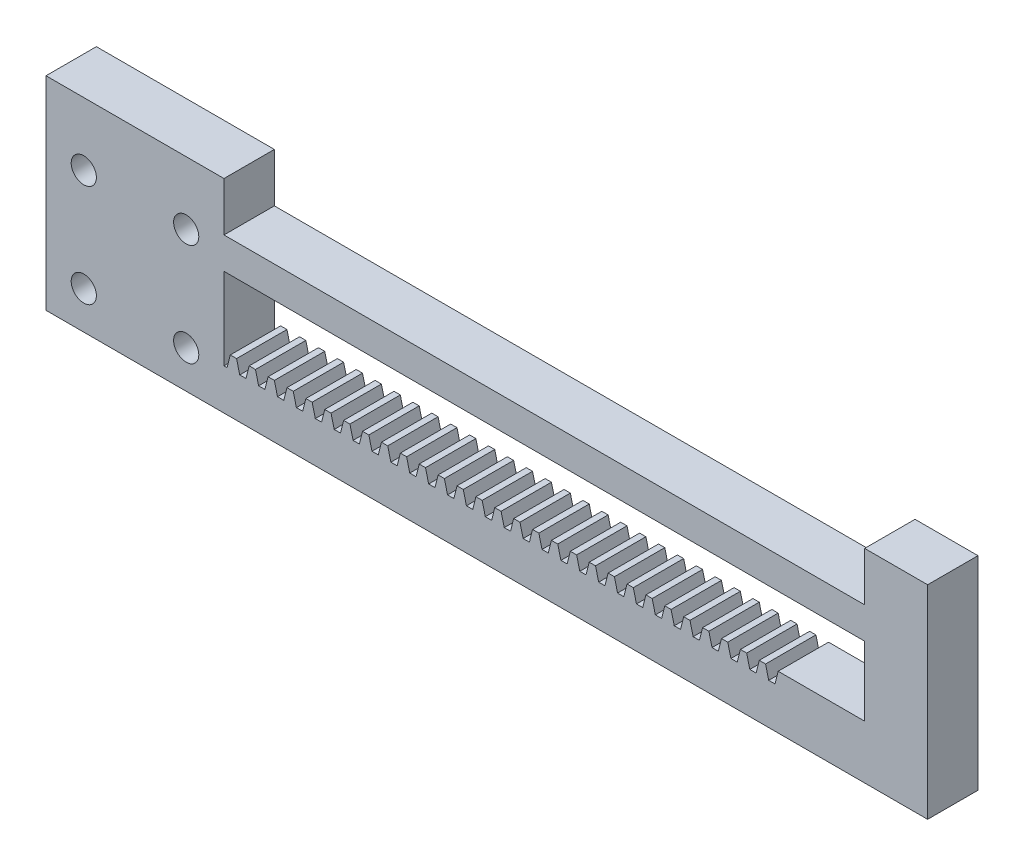
SolidWorks part; units mm, degrees
ref_plane "Front Plane" through (0, 0, 0) normal (0, 0, 1) x (1, 0, 0)
ref_plane "Top Plane" through (0, 0, 0) normal (0, 1, 0) x (1, 0, 0)
ref_plane "Right Plane" through (0, 0, 0) normal (1, 0, 0) x (0, 0, -1)
sketch "Sketch1" plane through (0, 0, 0) normal (0, 0, 1) x (1, 0, 0)
  line L1 (-111.7365, -14.1317) -> (-9.9686, -14.1317)
  line L2 (-111.7365, -7.6317) -> (-111.7365, 5.3683)
  line L4 (-10, -5.6317) -> (-10, 5.3683)
  line L5 (-111.7365, -7.6317) -> (-111.2365, -7.6317)
  line L6 (-111.2365, -7.6317) -> (-110.7365, -5.6317)
  line L7 (-111.7365, 18.1317) -> (-140, 18.1317)
  line L9 (-111.7365, -14.1317) -> (-140, -14.1317)
  line L15 (-10, 18.1317) -> (0, 18.1317) construction
  line L16 (-10, 18.1317) -> (-10, 10.3683) construction
  line L17 (-9.9686, -14.1317) -> (0, -14.1317) construction
  line L18 (0, 18.1317) -> (0, -14.1317)
  line L21 (-10, 18.1317) -> (0, 18.1317)
  line L22 (-10, -7.6317) -> (-111.7365, -7.6317) construction
  line L163 (-9.9686, -14.1317) -> (0, -14.1317)
  line L164 (-140, -14.1317) -> (-140, 18.1317)
  line L166 (-111.7365, -7.6317) -> (-111.7365, -14.1317) construction
  line L167 (-117.7365, -8.1317) -> (-134, 8.1317) construction
  line L168 (-134, -8.1317) -> (-117.7365, 8.1317) construction
  line L169 (-23.7365, -5.6317) -> (-10, -5.6317)
  line L170 (-135.8069, 0) -> (-111.7365, 0) construction
  line L171 (-111.7365, 5.3683) -> (-10, 5.3683)
  line L181 (-110.7365, -5.6317) -> (-109.7365, -5.6317)
  line L182 (-109.7365, -5.6317) -> (-109.2365, -7.6317)
  line L183 (-109.2365, -7.6317) -> (-108.7365, -7.6317)
  line L185 (-111.2365, -7.6317) -> (-109.2365, -7.6317) construction
  line L187 (-110.2365, -7.6317) -> (-110.2365, -5.6317) construction
  line L189 (-108.7365, -7.6317) -> (-108.2365, -7.6317)
  line L190 (-108.2365, -7.6317) -> (-107.7365, -5.6317)
  line L191 (-107.7365, -5.6317) -> (-106.7365, -5.6317)
  line L192 (-106.7365, -5.6317) -> (-106.2365, -7.6317)
  line L193 (-106.2365, -7.6317) -> (-105.7365, -7.6317)
  line L194 (-105.7365, -7.6317) -> (-105.2365, -7.6317)
  line L195 (-105.2365, -7.6317) -> (-104.7365, -5.6317)
  line L196 (-104.7365, -5.6317) -> (-103.7365, -5.6317)
  line L197 (-103.7365, -5.6317) -> (-103.2365, -7.6317)
  line L198 (-103.2365, -7.6317) -> (-102.7365, -7.6317)
  line L199 (-102.7365, -7.6317) -> (-102.2365, -7.6317)
  line L200 (-102.2365, -7.6317) -> (-101.7365, -5.6317)
  line L201 (-101.7365, -5.6317) -> (-100.7365, -5.6317)
  line L202 (-100.7365, -5.6317) -> (-100.2365, -7.6317)
  line L203 (-100.2365, -7.6317) -> (-99.7365, -7.6317)
  line L204 (-99.7365, -7.6317) -> (-99.2365, -7.6317)
  line L205 (-99.2365, -7.6317) -> (-98.7365, -5.6317)
  line L206 (-98.7365, -5.6317) -> (-97.7365, -5.6317)
  line L207 (-97.7365, -5.6317) -> (-97.2365, -7.6317)
  line L208 (-97.2365, -7.6317) -> (-96.7365, -7.6317)
  line L209 (-96.7365, -7.6317) -> (-96.2365, -7.6317)
  line L210 (-96.2365, -7.6317) -> (-95.7365, -5.6317)
  line L211 (-95.7365, -5.6317) -> (-94.7365, -5.6317)
  line L212 (-94.7365, -5.6317) -> (-94.2365, -7.6317)
  line L213 (-94.2365, -7.6317) -> (-93.7365, -7.6317)
  line L214 (-93.7365, -7.6317) -> (-93.2365, -7.6317)
  line L215 (-93.2365, -7.6317) -> (-92.7365, -5.6317)
  line L216 (-92.7365, -5.6317) -> (-91.7365, -5.6317)
  line L217 (-91.7365, -5.6317) -> (-91.2365, -7.6317)
  line L218 (-91.2365, -7.6317) -> (-90.7365, -7.6317)
  line L219 (-90.7365, -7.6317) -> (-90.2365, -7.6317)
  line L220 (-90.2365, -7.6317) -> (-89.7365, -5.6317)
  line L221 (-89.7365, -5.6317) -> (-88.7365, -5.6317)
  line L222 (-88.7365, -5.6317) -> (-88.2365, -7.6317)
  line L223 (-88.2365, -7.6317) -> (-87.7365, -7.6317)
  line L224 (-87.7365, -7.6317) -> (-87.2365, -7.6317)
  line L225 (-87.2365, -7.6317) -> (-86.7365, -5.6317)
  line L226 (-86.7365, -5.6317) -> (-85.7365, -5.6317)
  line L227 (-85.7365, -5.6317) -> (-85.2365, -7.6317)
  line L228 (-85.2365, -7.6317) -> (-84.7365, -7.6317)
  line L229 (-84.7365, -7.6317) -> (-84.2365, -7.6317)
  line L230 (-84.2365, -7.6317) -> (-83.7365, -5.6317)
  line L231 (-83.7365, -5.6317) -> (-82.7365, -5.6317)
  line L232 (-82.7365, -5.6317) -> (-82.2365, -7.6317)
  line L233 (-82.2365, -7.6317) -> (-81.7365, -7.6317)
  line L234 (-81.7365, -7.6317) -> (-81.2365, -7.6317)
  line L235 (-81.2365, -7.6317) -> (-80.7365, -5.6317)
  line L236 (-80.7365, -5.6317) -> (-79.7365, -5.6317)
  line L237 (-79.7365, -5.6317) -> (-79.2365, -7.6317)
  line L238 (-79.2365, -7.6317) -> (-78.7365, -7.6317)
  line L239 (-78.7365, -7.6317) -> (-78.2365, -7.6317)
  line L240 (-78.2365, -7.6317) -> (-77.7365, -5.6317)
  line L241 (-77.7365, -5.6317) -> (-76.7365, -5.6317)
  line L242 (-76.7365, -5.6317) -> (-76.2365, -7.6317)
  line L243 (-76.2365, -7.6317) -> (-75.7365, -7.6317)
  line L244 (-75.7365, -7.6317) -> (-75.2365, -7.6317)
  line L245 (-75.2365, -7.6317) -> (-74.7365, -5.6317)
  line L246 (-74.7365, -5.6317) -> (-73.7365, -5.6317)
  line L247 (-73.7365, -5.6317) -> (-73.2365, -7.6317)
  line L248 (-73.2365, -7.6317) -> (-72.7365, -7.6317)
  line L249 (-72.7365, -7.6317) -> (-72.2365, -7.6317)
  line L250 (-72.2365, -7.6317) -> (-71.7365, -5.6317)
  line L251 (-71.7365, -5.6317) -> (-70.7365, -5.6317)
  line L252 (-70.7365, -5.6317) -> (-70.2365, -7.6317)
  line L253 (-70.2365, -7.6317) -> (-69.7365, -7.6317)
  line L254 (-69.7365, -7.6317) -> (-69.2365, -7.6317)
  line L255 (-69.2365, -7.6317) -> (-68.7365, -5.6317)
  line L256 (-68.7365, -5.6317) -> (-67.7365, -5.6317)
  line L257 (-67.7365, -5.6317) -> (-67.2365, -7.6317)
  line L258 (-67.2365, -7.6317) -> (-66.7365, -7.6317)
  line L259 (-66.7365, -7.6317) -> (-66.2365, -7.6317)
  line L260 (-66.2365, -7.6317) -> (-65.7365, -5.6317)
  line L261 (-65.7365, -5.6317) -> (-64.7365, -5.6317)
  line L262 (-64.7365, -5.6317) -> (-64.2365, -7.6317)
  line L263 (-64.2365, -7.6317) -> (-63.7365, -7.6317)
  line L264 (-63.7365, -7.6317) -> (-63.2365, -7.6317)
  line L265 (-63.2365, -7.6317) -> (-62.7365, -5.6317)
  line L266 (-62.7365, -5.6317) -> (-61.7365, -5.6317)
  line L267 (-61.7365, -5.6317) -> (-61.2365, -7.6317)
  line L268 (-61.2365, -7.6317) -> (-60.7365, -7.6317)
  line L269 (-60.7365, -7.6317) -> (-60.2365, -7.6317)
  line L270 (-60.2365, -7.6317) -> (-59.7365, -5.6317)
  line L271 (-59.7365, -5.6317) -> (-58.7365, -5.6317)
  line L272 (-58.7365, -5.6317) -> (-58.2365, -7.6317)
  line L273 (-58.2365, -7.6317) -> (-57.7365, -7.6317)
  line L274 (-57.7365, -7.6317) -> (-57.2365, -7.6317)
  line L275 (-57.2365, -7.6317) -> (-56.7365, -5.6317)
  line L276 (-56.7365, -5.6317) -> (-55.7365, -5.6317)
  line L277 (-55.7365, -5.6317) -> (-55.2365, -7.6317)
  line L278 (-55.2365, -7.6317) -> (-54.7365, -7.6317)
  line L279 (-54.7365, -7.6317) -> (-54.2365, -7.6317)
  line L280 (-54.2365, -7.6317) -> (-53.7365, -5.6317)
  line L281 (-53.7365, -5.6317) -> (-52.7365, -5.6317)
  line L282 (-52.7365, -5.6317) -> (-52.2365, -7.6317)
  line L283 (-52.2365, -7.6317) -> (-51.7365, -7.6317)
  line L284 (-51.7365, -7.6317) -> (-51.2365, -7.6317)
  line L285 (-51.2365, -7.6317) -> (-50.7365, -5.6317)
  line L286 (-50.7365, -5.6317) -> (-49.7365, -5.6317)
  line L287 (-49.7365, -5.6317) -> (-49.2365, -7.6317)
  line L288 (-49.2365, -7.6317) -> (-48.7365, -7.6317)
  line L289 (-48.7365, -7.6317) -> (-48.2365, -7.6317)
  line L290 (-48.2365, -7.6317) -> (-47.7365, -5.6317)
  line L291 (-47.7365, -5.6317) -> (-46.7365, -5.6317)
  line L292 (-46.7365, -5.6317) -> (-46.2365, -7.6317)
  line L293 (-46.2365, -7.6317) -> (-45.7365, -7.6317)
  line L294 (-45.7365, -7.6317) -> (-45.2365, -7.6317)
  line L295 (-45.2365, -7.6317) -> (-44.7365, -5.6317)
  line L296 (-44.7365, -5.6317) -> (-43.7365, -5.6317)
  line L297 (-43.7365, -5.6317) -> (-43.2365, -7.6317)
  line L298 (-43.2365, -7.6317) -> (-42.7365, -7.6317)
  line L299 (-42.7365, -7.6317) -> (-42.2365, -7.6317)
  line L300 (-42.2365, -7.6317) -> (-41.7365, -5.6317)
  line L301 (-41.7365, -5.6317) -> (-40.7365, -5.6317)
  line L302 (-40.7365, -5.6317) -> (-40.2365, -7.6317)
  line L303 (-40.2365, -7.6317) -> (-39.7365, -7.6317)
  line L304 (-39.7365, -7.6317) -> (-39.2365, -7.6317)
  line L305 (-39.2365, -7.6317) -> (-38.7365, -5.6317)
  line L306 (-38.7365, -5.6317) -> (-37.7365, -5.6317)
  line L307 (-37.7365, -5.6317) -> (-37.2365, -7.6317)
  line L308 (-37.2365, -7.6317) -> (-36.7365, -7.6317)
  line L309 (-36.7365, -7.6317) -> (-36.2365, -7.6317)
  line L310 (-36.2365, -7.6317) -> (-35.7365, -5.6317)
  line L311 (-35.7365, -5.6317) -> (-34.7365, -5.6317)
  line L312 (-34.7365, -5.6317) -> (-34.2365, -7.6317)
  line L313 (-34.2365, -7.6317) -> (-33.7365, -7.6317)
  line L314 (-33.7365, -7.6317) -> (-33.2365, -7.6317)
  line L315 (-33.2365, -7.6317) -> (-32.7365, -5.6317)
  line L316 (-32.7365, -5.6317) -> (-31.7365, -5.6317)
  line L317 (-31.7365, -5.6317) -> (-31.2365, -7.6317)
  line L318 (-31.2365, -7.6317) -> (-30.7365, -7.6317)
  line L319 (-30.7365, -7.6317) -> (-30.2365, -7.6317)
  line L320 (-30.2365, -7.6317) -> (-29.7365, -5.6317)
  line L321 (-29.7365, -5.6317) -> (-28.7365, -5.6317)
  line L322 (-28.7365, -5.6317) -> (-28.2365, -7.6317)
  line L323 (-28.2365, -7.6317) -> (-27.7365, -7.6317)
  line L324 (-27.7365, -7.6317) -> (-27.2365, -7.6317)
  line L325 (-27.2365, -7.6317) -> (-26.7365, -5.6317)
  line L326 (-26.7365, -5.6317) -> (-25.7365, -5.6317)
  line L327 (-25.7365, -5.6317) -> (-25.2365, -7.6317)
  line L328 (-25.2365, -7.6317) -> (-24.7365, -7.6317)
  line L329 (-24.7365, -7.6317) -> (-24.2365, -7.6317)
  line L330 (-24.2365, -7.6317) -> (-23.7365, -5.6317)
  line L415 (13.7635, -7.6317) -> (14.2635, -7.6317) [skipped]
  line L416 (14.2635, -7.6317) -> (14.7635, -7.6317) [skipped]
  line L417 (14.7635, -7.6317) -> (15.2635, -5.6317) [skipped]
  line L418 (15.2635, -5.6317) -> (16.2635, -5.6317) [skipped]
  line L419 (16.2635, -5.6317) -> (16.7635, -7.6317) [skipped]
  line L420 (16.7635, -7.6317) -> (17.2635, -7.6317) [skipped]
  line L421 (17.2635, -7.6317) -> (17.7635, -7.6317) [skipped]
  line L422 (17.7635, -7.6317) -> (18.2635, -5.6317) [skipped]
  line L423 (18.2635, -5.6317) -> (19.2635, -5.6317) [skipped]
  line L424 (19.2635, -5.6317) -> (19.7635, -7.6317) [skipped]
  line L425 (19.7635, -7.6317) -> (20.2635, -7.6317) [skipped]
  line L426 (20.2635, -7.6317) -> (20.7635, -7.6317) [skipped]
  line L427 (20.7635, -7.6317) -> (21.2635, -5.6317) [skipped]
  line L428 (21.2635, -5.6317) -> (22.2635, -5.6317) [skipped]
  line L429 (22.2635, -5.6317) -> (22.7635, -7.6317) [skipped]
  line L430 (22.7635, -7.6317) -> (23.2635, -7.6317) [skipped]
  line L431 (23.2635, -7.6317) -> (23.7635, -7.6317) [skipped]
  line L432 (23.7635, -7.6317) -> (24.2635, -5.6317) [skipped]
  line L433 (24.2635, -5.6317) -> (25.2635, -5.6317) [skipped]
  line L434 (25.2635, -5.6317) -> (25.7635, -7.6317) [skipped]
  line L435 (25.7635, -7.6317) -> (26.2635, -7.6317) [skipped]
  line L436 (13.2635, -5.6317) -> (13.7635, -7.6317) [skipped]
  line L437 (11.7635, -7.6317) -> (12.2635, -5.6317) [skipped]
  line L438 (12.2635, -5.6317) -> (13.2635, -5.6317) [skipped]
  line L440 (8.7635, -7.6317) -> (9.2635, -5.6317) [skipped]
  line L441 (9.2635, -5.6317) -> (10.2635, -5.6317) [skipped]
  line L442 (10.2635, -5.6317) -> (10.7635, -7.6317) [skipped]
  line L443 (10.7635, -7.6317) -> (11.2635, -7.6317) [skipped]
  line L444 (11.2635, -7.6317) -> (11.7635, -7.6317) [skipped]
  line L445 (8.2635, -7.6317) -> (8.7635, -7.6317) [skipped]
  line L446 (7.7635, -7.6317) -> (8.2635, -7.6317) [skipped]
  line L447 (-111.7365, 10.3683) -> (-10, 10.3683)
  line L448 (-111.7365, 10.3683) -> (-111.7365, 18.1317)
  line L449 (-10.7365, -5.6317) -> (-10.2365, -7.6317) [skipped]
  line L450 (-10.2365, -7.6317) -> (-9.7365, -7.6317) [skipped]
  line L451 (-9.7365, -7.6317) -> (-9.2365, -7.6317) [skipped]
  line L452 (-9.2365, -7.6317) -> (-8.7365, -5.6317) [skipped]
  line L453 (-8.7365, -5.6317) -> (-7.7365, -5.6317) [skipped]
  line L454 (-7.7365, -5.6317) -> (-7.2365, -7.6317) [skipped]
  line L455 (-7.2365, -7.6317) -> (-6.7365, -7.6317) [skipped]
  line L456 (-6.7365, -7.6317) -> (-6.2365, -7.6317) [skipped]
  line L457 (-6.2365, -7.6317) -> (-5.7365, -5.6317) [skipped]
  line L458 (-5.7365, -5.6317) -> (-4.7365, -5.6317) [skipped]
  line L459 (-4.7365, -5.6317) -> (-4.2365, -7.6317) [skipped]
  line L460 (-4.2365, -7.6317) -> (-3.7365, -7.6317) [skipped]
  line L461 (-3.7365, -7.6317) -> (-3.2365, -7.6317) [skipped]
  line L462 (-3.2365, -7.6317) -> (-2.7365, -5.6317) [skipped]
  line L463 (-2.7365, -5.6317) -> (-1.7365, -5.6317) [skipped]
  line L464 (-1.7365, -5.6317) -> (-1.2365, -7.6317) [skipped]
  line L465 (-1.2365, -7.6317) -> (-0.7365, -7.6317) [skipped]
  line L466 (-0.7365, -7.6317) -> (-0.2365, -7.6317) [skipped]
  line L467 (-0.2365, -7.6317) -> (0.2635, -5.6317) [skipped]
  line L468 (0.2635, -5.6317) -> (1.2635, -5.6317) [skipped]
  line L469 (1.2635, -5.6317) -> (1.7635, -7.6317) [skipped]
  line L470 (1.7635, -7.6317) -> (2.2635, -7.6317) [skipped]
  line L471 (2.2635, -7.6317) -> (2.7635, -7.6317) [skipped]
  line L472 (2.7635, -7.6317) -> (3.2635, -5.6317) [skipped]
  line L473 (3.2635, -5.6317) -> (4.2635, -5.6317) [skipped]
  line L474 (4.2635, -5.6317) -> (4.7635, -7.6317) [skipped]
  line L475 (4.7635, -7.6317) -> (5.2635, -7.6317) [skipped]
  line L476 (5.2635, -7.6317) -> (5.7635, -7.6317) [skipped]
  line L477 (5.7635, -7.6317) -> (6.2635, -5.6317) [skipped]
  line L478 (6.2635, -5.6317) -> (7.2635, -5.6317) [skipped]
  line L479 (7.2635, -5.6317) -> (7.7635, -7.6317) [skipped]
  line L480 (-17.7365, -5.6317) -> (-16.7365, -5.6317) [skipped]
  line L481 (-16.7365, -5.6317) -> (-16.2365, -7.6317) [skipped]
  line L482 (-16.2365, -7.6317) -> (-15.7365, -7.6317) [skipped]
  line L483 (-15.7365, -7.6317) -> (-15.2365, -7.6317) [skipped]
  line L484 (-15.2365, -7.6317) -> (-14.7365, -5.6317) [skipped]
  line L485 (-14.7365, -5.6317) -> (-13.7365, -5.6317) [skipped]
  line L486 (-13.7365, -5.6317) -> (-13.2365, -7.6317) [skipped]
  line L487 (-13.2365, -7.6317) -> (-12.7365, -7.6317) [skipped]
  line L488 (-12.7365, -7.6317) -> (-12.2365, -7.6317) [skipped]
  line L489 (-12.2365, -7.6317) -> (-11.7365, -5.6317) [skipped]
  line L490 (-11.7365, -5.6317) -> (-10.7365, -5.6317) [skipped]
  line L491 (-20.7365, -5.6317) -> (-19.7365, -5.6317) [skipped]
  line L492 (-19.7365, -5.6317) -> (-19.2365, -7.6317) [skipped]
  line L493 (-19.2365, -7.6317) -> (-18.7365, -7.6317) [skipped]
  line L494 (-18.7365, -7.6317) -> (-18.2365, -7.6317) [skipped]
  line L495 (-18.2365, -7.6317) -> (-17.7365, -5.6317) [skipped]
  line L496 (-22.2365, -7.6317) -> (-21.7365, -7.6317) [skipped]
  line L497 (-21.7365, -7.6317) -> (-21.2365, -7.6317) [skipped]
  line L498 (-21.2365, -7.6317) -> (-20.7365, -5.6317) [skipped]
  line L499 (-22.7365, -5.6317) -> (-22.2365, -7.6317) [skipped]
  line L500 (-23.7365, -5.6317) -> (-22.7365, -5.6317) [skipped]
  line L501 (-10, 10.3683) -> (-10, 18.1317)
  line L502 (-10, 5.3683) -> (-10, -5.6317) construction
  circle A0 centre (-134, 8.1317) radius 2
  circle A1 centre (-117.7365, 8.1317) radius 2
  circle A2 centre (-134, -8.1317) radius 2
  circle A3 centre (-117.7365, -8.1317) radius 2
  circle A4 centre (-58.7365, -2.6317) radius 5 construction
  point P20 (-125.8683, 0)
  point P56 (0, 0)
  point P62 (0, 0)
  point P68 (-135.8069, 0)
  point P238 (-123.7717, 0)
  dimension "D2" = 4
  dimension "D12" = 6
  dimension "D15" = 10
  dimension "D16" = 8
  dimension "D3" = 3
  dimension "D4" = 0.5
  dimension "D5" = 140
  dimension "D7" = 6
  dimension "D8" = 23
  dimension "D6" = 24.5
  dimension "D9" = 1
  dimension "D10" = 2
  dimension "D13" = 6
  dimension "D14" = 10
  dimension "D17" = 10
  dimension "D18" = 5
  dimension "D11" = 46
extrude "Boss-Extrude1" add sketch "Sketch1" along normal blind 8
